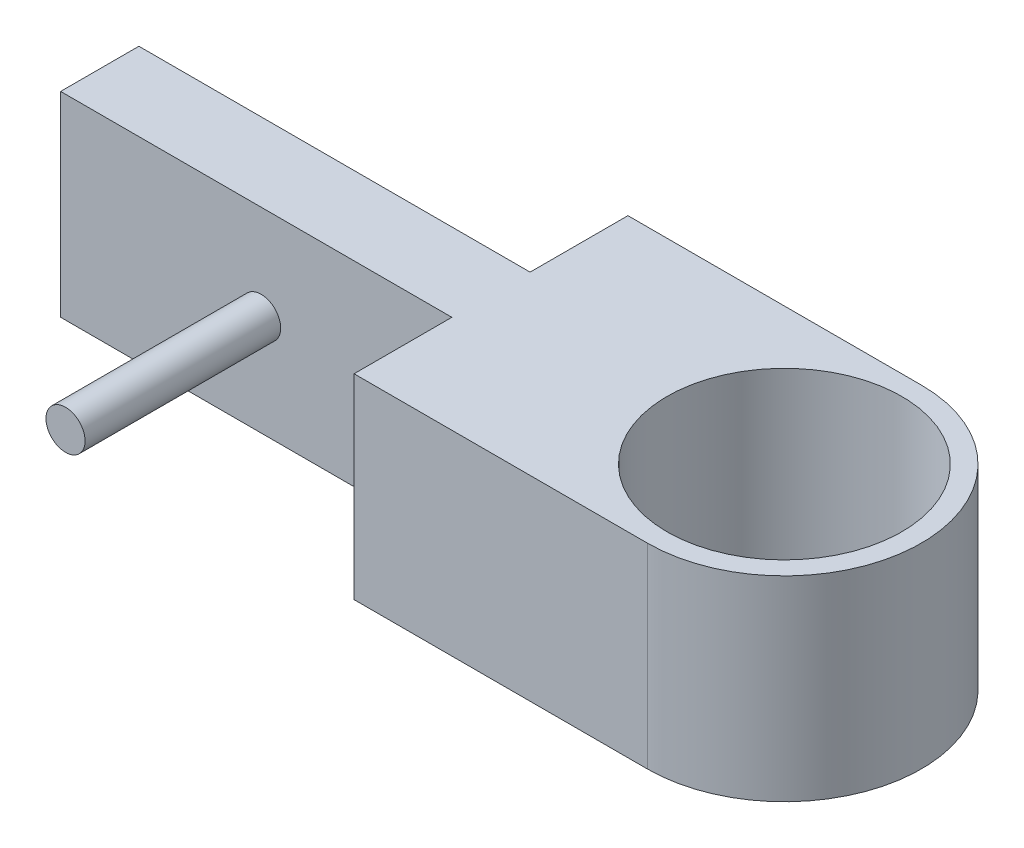
SolidWorks part; units mm, degrees
ref_plane "Alzado" through (0, 0, 0) normal (0, 0, 1) x (1, 0, 0)
ref_plane "Planta" through (0, 0, 0) normal (0, 1, 0) x (1, 0, 0)
ref_plane "Vista lateral" through (0, 0, 0) normal (1, 0, 0) x (0, 0, -1)
sketch "Croquis2" plane through (0, 0, 0) normal (0, 1, 0) x (1, 0, 0)
  line L0 (-41.7727, 29.3019) -> (-56.7727, 29.3019)
  line L1 (-66.7727, 20.3019) -> (-76.7727, 20.3019)
  line L2 (-56.7727, 15.3019) -> (-41.7727, 15.3019)
  line L3 (-56.7727, 29.3019) -> (-56.7727, 24.3019)
  line L4 (-56.7727, 20.3019) -> (-56.7727, 15.3019)
  line L5 (-66.7727, 24.3019) -> (-56.7727, 24.3019)
  line L7 (-56.7727, 20.3019) -> (-66.7727, 20.3019)
  line L10 (-76.7727, 20.3019) -> (-76.7727, 24.3019)
  line L11 (-76.7727, 24.3019) -> (-66.7727, 24.3019)
  circle A0 centre (-41.7727, 22.3019) radius 6
  circle A1 centre (-41.7727, 22.3019) radius 7
  dimension "D1" = 15
  dimension "D3" = 20
  dimension "D2" = 14
  dimension "D4" = 4
  dimension "D5" = 5
  dimension "D6" = 5
extrude "Saliente-Extruir3" add sketch "Croquis2" along normal blind 10 contours A1 L0 L3 L5 L11 L10 L1 L7 L4 L2 | A0
sketch "Croquis9" plane through (0, 0, -20.3019) normal (0, 0, 1) x (1, 0, 0)
  circle A0 centre (-66.5226, 5.1453) radius 1
extrude "Saliente-Extruir6" add sketch "Croquis9" along normal blind 10
